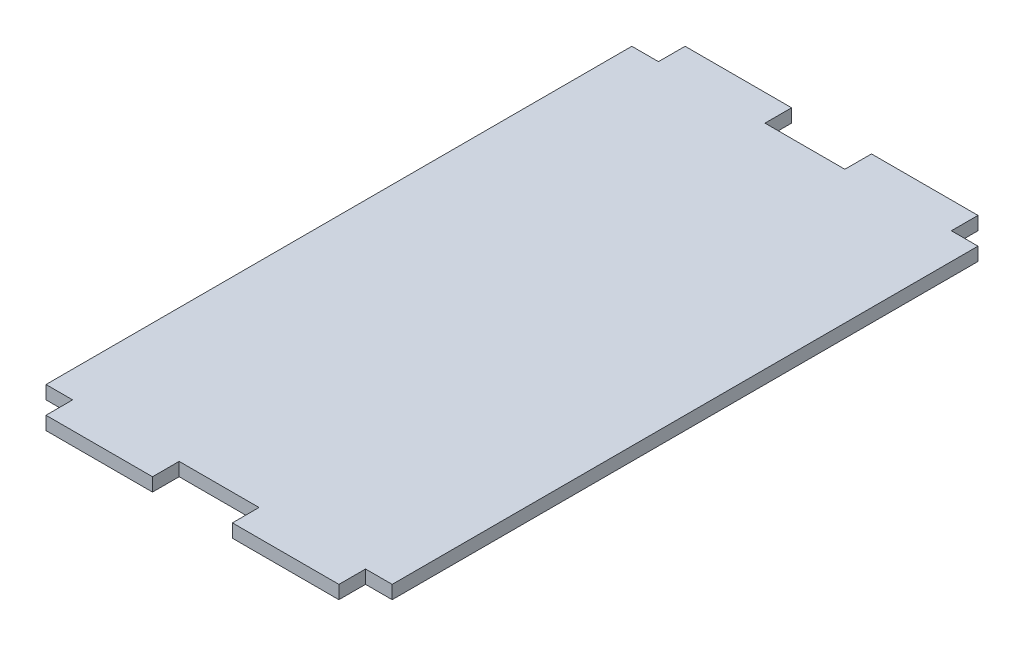
SolidWorks part; units mm, degrees
material "Cedar"
ref_plane "Front Plane" through (0, 0, 0) normal (0, 0, 1) x (1, 0, 0)
ref_plane "Top Plane" through (0, 0, 0) normal (0, 1, 0) x (1, 0, 0)
ref_plane "Right Plane" through (0, 0, 0) normal (1, 0, 0) x (0, 0, -1)
sketch "Sketch1" plane through (0, 0, 0) normal (0, 1, 0) x (1, 0, 0)
  line L1 (-41.275, 76.2) -> (41.275, 76.2)
  line L2 (-41.275, 76.2) -> (-41.275, -76.2)
  line L3 (-41.275, -76.2) -> (41.275, -76.2)
  line L4 (41.275, 76.2) -> (41.275, -76.2)
  line L5 (-41.275, 76.2) -> (41.275, -76.2) construction
  line L6 (-41.275, -76.2) -> (41.275, 76.2) construction
  point P0 (0, 0)
  dimension "D1" = 82.55
  dimension "D2" = 152.4
extrude "Boss-Extrude1" add sketch "Sketch1" along normal blind 3.175
sketch "Sketch2" plane through (0, 3.175, 0) normal (0, 1, 0) x (1, 0, 0)
  line L0 (-41.275, -69.85) -> (41.275, -69.85) construction
  line L1 (-41.275, 76.2) -> (-41.275, -76.2) construction
  line L2 (41.275, -76.2) -> (41.275, 76.2) construction
  line L3 (0, -76.2) -> (0, -69.85) construction
  line L4 (-41.275, -76.2) -> (41.275, -76.2) construction
  line L5 (-34.925, -69.85) -> (-41.275, -69.85)
  line L6 (-34.925, -69.85) -> (-9.525, -69.85) construction
  line L7 (-34.925, -69.85) -> (-34.925, -76.2)
  line L8 (-34.925, -76.2) -> (-9.525, -76.2) construction
  line L9 (-9.525, -69.85) -> (-9.525, -76.2)
  line L10 (-34.925, -69.85) -> (-9.525, -76.2) construction
  line L11 (-34.925, -76.2) -> (-9.525, -69.85) construction
  line L12 (-41.275, -69.85) -> (-41.275, -76.2)
  line L13 (-41.275, -76.2) -> (-34.925, -76.2)
  line L14 (-9.525, -76.2) -> (9.525, -76.2)
  line L15 (0, -76.2) -> (0, -69.85)
  line L16 (9.525, -69.85) -> (-9.525, -69.85)
  line L17 (34.925, -76.2) -> (9.525, -69.85) construction
  line L18 (34.925, -69.85) -> (9.525, -76.2) construction
  line L19 (34.925, -76.2) -> (9.525, -76.2) construction
  line L20 (34.925, -69.85) -> (9.525, -69.85) construction
  line L21 (41.275, -76.2) -> (34.925, -76.2)
  line L22 (41.275, -69.85) -> (41.275, -76.2)
  line L23 (9.525, -69.85) -> (9.525, -76.2)
  line L24 (34.925, -69.85) -> (34.925, -76.2)
  line L25 (34.925, -69.85) -> (41.275, -69.85)
  point P10 (-22.225, -73.025)
  point P22 (22.225, -73.025)
  line M12 (41.275, -76.2) -> (41.275, 76.2)
  line M14 (-41.275, 76.2) -> (-41.275, -76.2)
  line M15 (-41.275, -76.2) -> (41.275, -76.2)
  dimension "D1" = 6.35
  dimension "D2" = 9.525
  dimension "D3" = 25.4
extrude "Cut-Extrude1" cut sketch "Sketch2" against normal through all contours L7 L5 M14 M15 | L15 L16 L9 M15 | L23 L16 L15 L14 | L25 L24 M15 M12
mirror "Mirror1" about plane through (0, 0, 0) normal (0, 0, 1) of "Cut-Extrude1"
